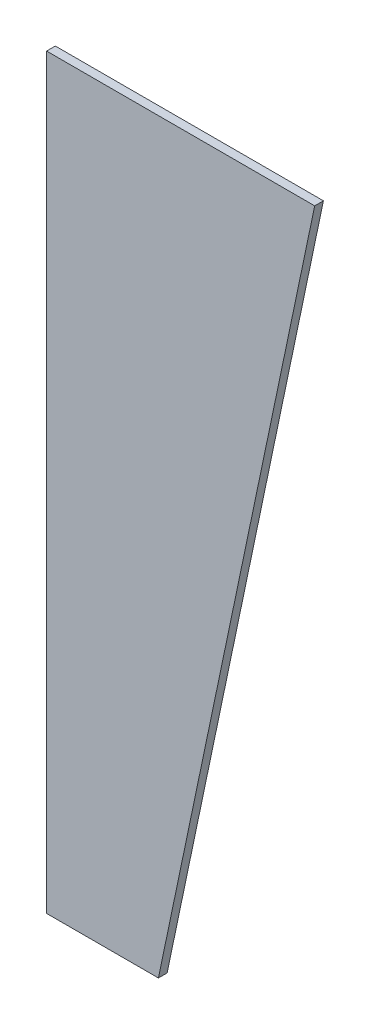
SolidWorks part; units mm, degrees
ref_plane "Front Plane" through (0, 0, 0) normal (0, 0, 1) x (1, 0, 0)
ref_plane "Top Plane" through (0, 0, 0) normal (0, 1, 0) x (1, 0, 0)
ref_plane "Right Plane" through (0, 0, 0) normal (1, 0, 0) x (0, 0, -1)
sketch "Sketch1" plane through (0, 0, 0) normal (0, 0, 1) x (1, 0, 0)
  line L0 (0, 0) -> (0, 257)
  line L1 (0, 0) -> (38.48, 0)
  line L2 (38.48, 0) -> (92.26, 257)
  line L3 (0, 257) -> (92.26, 257)
  line L4 (92.26, 257) -> (93.5696, 258.7594)
extrude "Boss-Extrude1" add sketch "Sketch1" along normal blind 3 contours L3 L0 L1 L2
